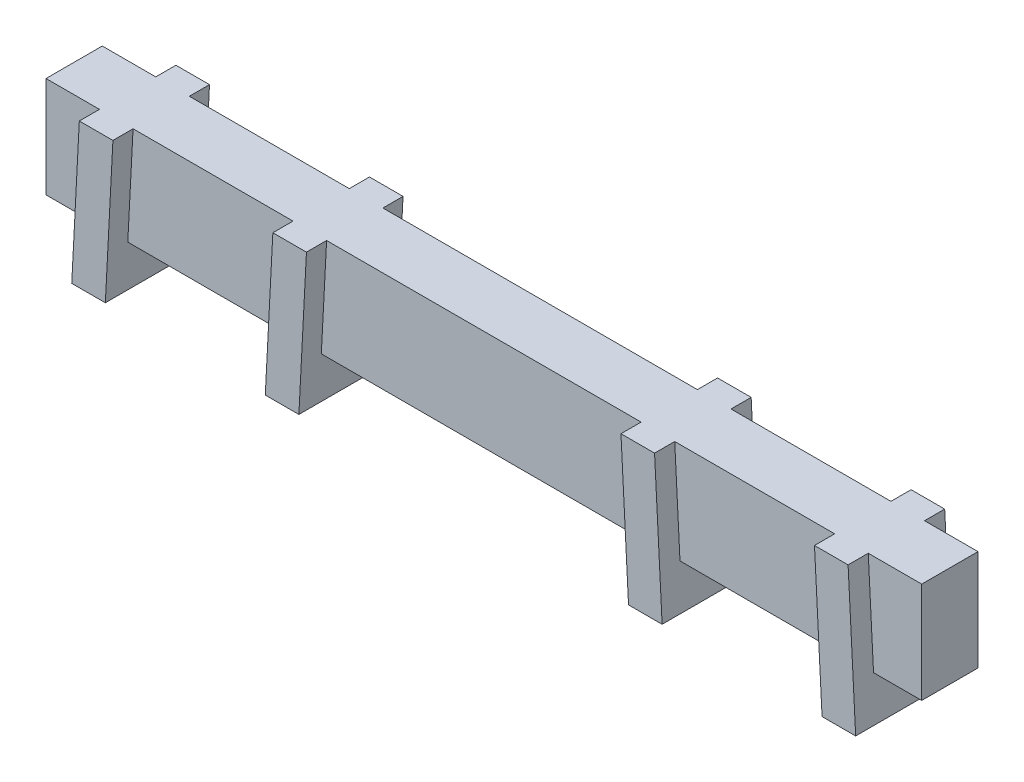
SolidWorks part; units mm, degrees
ref_plane "Front Plane" through (0, 0, 0) normal (0, 0, 1) x (1, 0, 0)
ref_plane "Top Plane" through (0, 0, 0) normal (0, 1, 0) x (1, 0, 0)
ref_plane "Right Plane" through (0, 0, 0) normal (1, 0, 0) x (0, 0, -1)
sketch "Sketch1" plane through (0, 0, 0) normal (0, 1, 0) x (1, 0, 0)
  line L1 (-33.1, -4.2545) -> (33.1, -4.2545)
  line L2 (-33.1, -4.2545) -> (-33.1, 0)
  line L3 (-33.1, 0) -> (33.1, 0)
  line L4 (33.1, -4.2545) -> (33.1, 0)
  dimension "D1" = 4.2545
  dimension "D2" = 66.2
extrude "Boss-Extrude1" add sketch "Sketch1" along normal blind 7.62
sketch "Sketch2" plane through (0, 0, 0) normal (0, -1, 0) x (1, 0, 0)
  line L0 (-14.827, 4.2545) -> (-14.827, 0)
  line L1 (-33.1, 4.2545) -> (33.1, 4.2545) construction
  line L2 (33.1, 0) -> (-33.1, 0) construction
  line L3 (-26.9174, 4.2545) -> (-26.9174, 0)
  line L4 (14.827, 4.2545) -> (14.827, 0)
  line L5 (26.9174, 4.2545) -> (26.9174, 0)
  dimension "D1" = 14.827
  dimension "D2" = 26.9174
  dimension "D3" = 14.827
  dimension "D4" = 26.9174
ref_plane "Plane2" through (-26.8437, 1.4068, 0) normal (-0.9986, 0.0523, 0) x (0, 0, -1)
ref_plane "Plane3" through (-14.7864, 0.7749, 0) normal (-0.9986, 0.0523, 0) x (0, 0, -1)
ref_plane "Plane4" through (26.8437, 1.4068, 0) normal (0.9986, 0.0523, 0) x (0, 0, -1)
ref_plane "Plane5" through (14.7864, 0.7749, 0) normal (0.9986, 0.0523, 0) x (0, 0, -1)
sketch "Sketch3" plane through (-26.8437, 1.4068, 0) normal (-0.9986, 0.0523, 0) x (0, 0, -1)
  line L0 (-2.1273, 1.7323) -> (-2.1273, -10.9677) construction
  line L1 (-5.7785, 1.7323) -> (1.524, 1.7323)
  line L2 (-5.7785, 1.7323) -> (-5.7785, -10.9677)
  line L3 (-5.7785, -10.9677) -> (1.524, -10.9677)
  line L4 (1.524, 1.7323) -> (1.524, -10.9677)
  line L5 (-5.7785, -4.6177) -> (1.524, -4.6177) construction
  line L6 (0, 1.7323) -> (-4.2545, 1.7323) construction
  point P10 (-2.1273, -4.6177)
  dimension "D1" = 7.3025
  dimension "D2" = 12.7
extrude "Boss-Extrude2" add sketch "Sketch3" along direction (1, 0, 0) on the side of the normal blind 2.54
sketch "Sketch7" plane through (-14.7864, 0.7749, 0) normal (-0.9986, 0.0523, 0) x (0, 0, -1)
  line L0 (-2.1273, -1.8744) -> (-2.1273, -14.5744) construction
  line L1 (-5.7785, 1.7323) -> (-5.7785, -10.9677) construction
  line L5 (1.524, -1.8744) -> (-5.7785, -1.8744)
  line L6 (1.524, -1.8744) -> (1.524, -14.5744)
  line L7 (1.524, -14.5744) -> (-5.7785, -14.5744)
  line L8 (-5.7785, -1.8744) -> (-5.7785, -14.5744)
  line L9 (1.524, -8.2244) -> (-5.7785, -8.2244) construction
  line L14 (-5.7785, -10.9677) -> (1.524, -10.9677) construction
  dimension "D1" = 12.7
  dimension "D2" = 7.3025
  dimension "D3" = 3.6067
extrude "Boss-Extrude3" add sketch "Sketch7" along direction (1, 0, 0) on the side against the normal blind 2.54
sketch "Sketch8" plane through (14.7864, 0.7749, 0) normal (0.9986, 0.0523, 0) x (0, 0, -1)
  line L0 (1.524, 16.0423) -> (1.524, 3.4119) construction
  line L1 (-5.7785, 8.6919) -> (1.524, 8.6919)
  line L2 (-5.7785, 8.6919) -> (-5.7785, -4.0081)
  line L3 (-5.7785, -4.0081) -> (1.524, -4.0081)
  line L4 (1.524, 8.6919) -> (1.524, -4.0081)
  line L7 (-4.2545, -0.776) -> (0, -0.776) construction
  dimension "D1" = 12.7
  dimension "D2" = 7.3025
  dimension "D3" = 3.2321
extrude "Boss-Extrude4" add sketch "Sketch8" along direction (-1, 0, 0) on the side against the normal blind 2.54
sketch "Sketch9" plane through (26.8437, 1.4068, 0) normal (0.9986, 0.0523, 0) x (0, 0, -1)
  line L0 (1.524, -3.8752) -> (1.524, 8.8248) construction
  line L1 (-5.7785, 10.9677) -> (1.524, 10.9677)
  line L2 (-5.7785, 10.9677) -> (-5.7785, -1.7323)
  line L3 (-5.7785, -1.7323) -> (1.524, -1.7323)
  line L4 (1.524, 10.9677) -> (1.524, -1.7323)
  line L5 (1.524, 8.8248) -> (-5.7785, 8.8248) construction
  line L11 (-4.2545, -1.7323) -> (0, -1.7323) construction
  dimension "D1" = 0
extrude "Boss-Extrude5" add sketch "Sketch9" along direction (-1, 0, 0) on the side of the normal blind 2.54
sketch "Sketch10" plane through (0, 7.62, 0) normal (0, 1, 0) x (1, 0, 0)
  line L0 (-33.1, 0) -> (-33.1, -4.2545) construction
  line L1 (-33.1, 9.2603) -> (33.1, 9.2603)
  line L2 (-33.1, 9.2603) -> (-33.1, -11.4828)
  line L3 (-33.1, -11.4828) -> (33.1, -11.4828)
  line L4 (33.1, 9.2603) -> (33.1, -11.4828)
  line L5 (33.1, -4.2545) -> (33.1, 0) construction
  dimension "D1" = 20.7431
  dimension "D2" = 9.2603
extrude "Cut-Extrude1" cut sketch "Sketch10" along normal through all
sketch "Sketch11" plane through (0, -0.3231, 0) normal (0, -1, 0) x (-1, 0, 0)
  line L1 (29.4743, -5.7785) -> (26.9343, -5.7785)
  line L2 (29.4743, -5.7785) -> (29.4743, 1.524)
  line L3 (29.4743, 1.524) -> (26.9343, 1.524)
  line L4 (26.9343, -5.7785) -> (26.9343, 1.524)
sketch "Sketch12" plane through (0, 2.6468, 0) normal (0, -1, 0) x (1, 0, 0)
  line L1 (-14.6883, 5.7785) -> (-12.1483, 5.7785)
  line L2 (-14.6883, 5.7785) -> (-14.6883, -1.524)
  line L3 (-14.6883, -1.524) -> (-12.1483, -1.524)
  line L4 (-12.1483, 5.7785) -> (-12.1483, -1.524)
sketch "Sketch13" plane through (0, -3.2277, 0) normal (0, -1, 0) x (1, 0, 0)
  line L1 (12.4562, 5.7785) -> (14.9962, 5.7785)
  line L2 (12.4562, 5.7785) -> (12.4562, -1.524)
  line L3 (12.4562, -1.524) -> (14.9962, -1.524)
  line L4 (14.9962, 5.7785) -> (14.9962, -1.524)
sketch "Sketch14" plane through (0, -0.3231, 0) normal (0, -1, 0) x (1, 0, 0)
  line L1 (26.9343, 5.7785) -> (29.4743, 5.7785)
  line L2 (26.9343, 5.7785) -> (26.9343, -1.524)
  line L3 (26.9343, -1.524) -> (29.4743, -1.524)
  line L4 (29.4743, 5.7785) -> (29.4743, -1.524)
extrude "Boss-Extrude6" add sketch "Sketch11" along direction (0.0523, 0.9986, 0) on the side of the normal blind 2.9789
extrude "Boss-Extrude7" add sketch "Sketch12" along direction (0.0523, 0.9986, 0) on the side of the normal blind 5.9487
extrude "Boss-Extrude8" add sketch "Sketch13" along direction (0.0523, -0.9986, 0) on the side of the normal blind 0.0742
extrude "Boss-Extrude9" add sketch "Sketch14" along direction (0.0523, -0.9986, 0) on the side of the normal blind 2.9789
